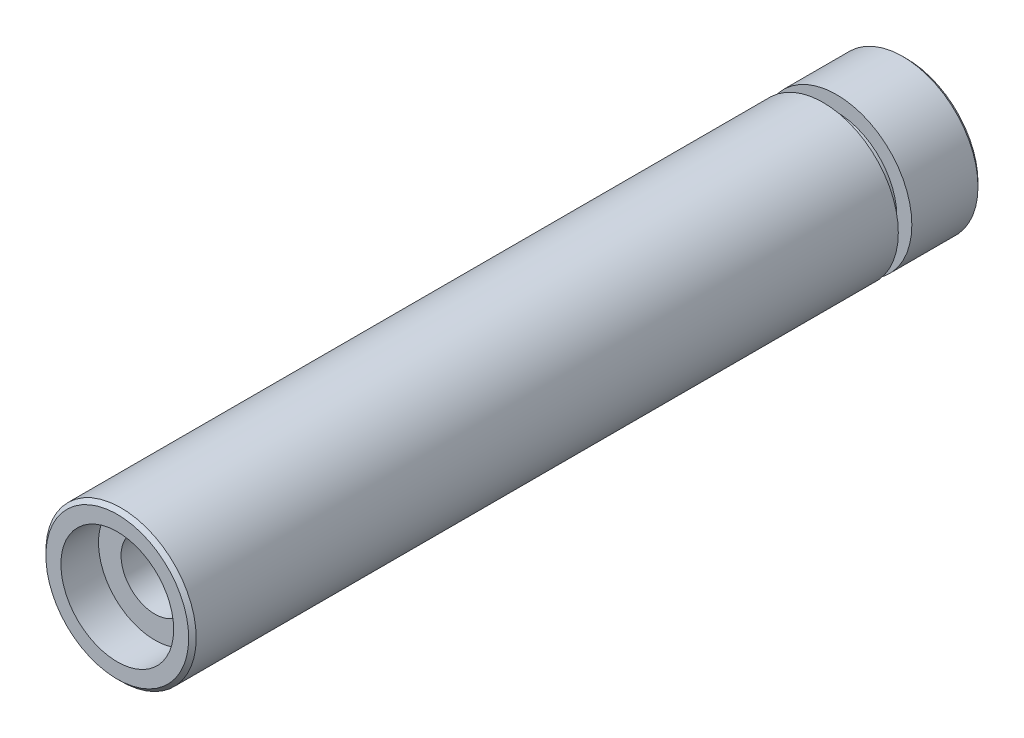
SolidWorks part; units mm, degrees
ref_plane "Front Plane" through (0, 0, 0) normal (0, 0, 1) x (1, 0, 0)
ref_plane "Top Plane" through (0, 0, 0) normal (0, 1, 0) x (1, 0, 0)
ref_plane "Right Plane" through (0, 0, 0) normal (1, 0, 0) x (0, 0, -1)
sketch "Sketch1" plane through (0, 0, 0) normal (0, 0, 1) x (1, 0, 0)
  circle A0 centre (0, 0) radius 10
  dimension "D1" = 20
extrude "Boss-Extrude1" add sketch "Sketch1" along normal blind 9.3
sketch "Sketch3" plane through (0, 0, 9.3) normal (0, 0, 1) x (1, 0, 0)
  circle A0 centre (0, 0) radius 8
  dimension "D1" = 16
extrude "Boss-Extrude2" add sketch "Sketch3" along normal blind 1.8
sketch "Sketch4" plane through (0, 0, 11.1) normal (0, 0, 1) x (1, 0, 0)
  circle A0 centre (0, 0) radius 10
  dimension "D1" = 20
extrude "Boss-Extrude3" add sketch "Sketch4" along normal blind 93.9
sketch "Sketch5" plane through (0, 0, 0) normal (0, 0, -1) x (-1, 0, 0)
  circle A0 centre (0, 0) radius 7.5
  dimension "D1" = 15
extrude "Cut-Extrude1" cut sketch "Sketch5" against normal blind 5
sketch "Sketch6" plane through (0, 0, 5) normal (0, 0, -1) x (-1, 0, 0)
  circle A0 centre (0, 0) radius 4.5
  dimension "D1" = 9
extrude "Cut-Extrude2" cut sketch "Sketch6" against normal blind 95
sketch "Sketch7" plane through (0, 0, 105) normal (0, 0, 1) x (1, 0, 0)
  circle A0 centre (0, 0) radius 7.5
  dimension "D1" = 15
extrude "Cut-Extrude3" cut sketch "Sketch7" against normal blind 5
chamfer "Chamfer1" distance 0.5 angle 45 2 edges at (10, 0, 105) (10, 0, 0)
